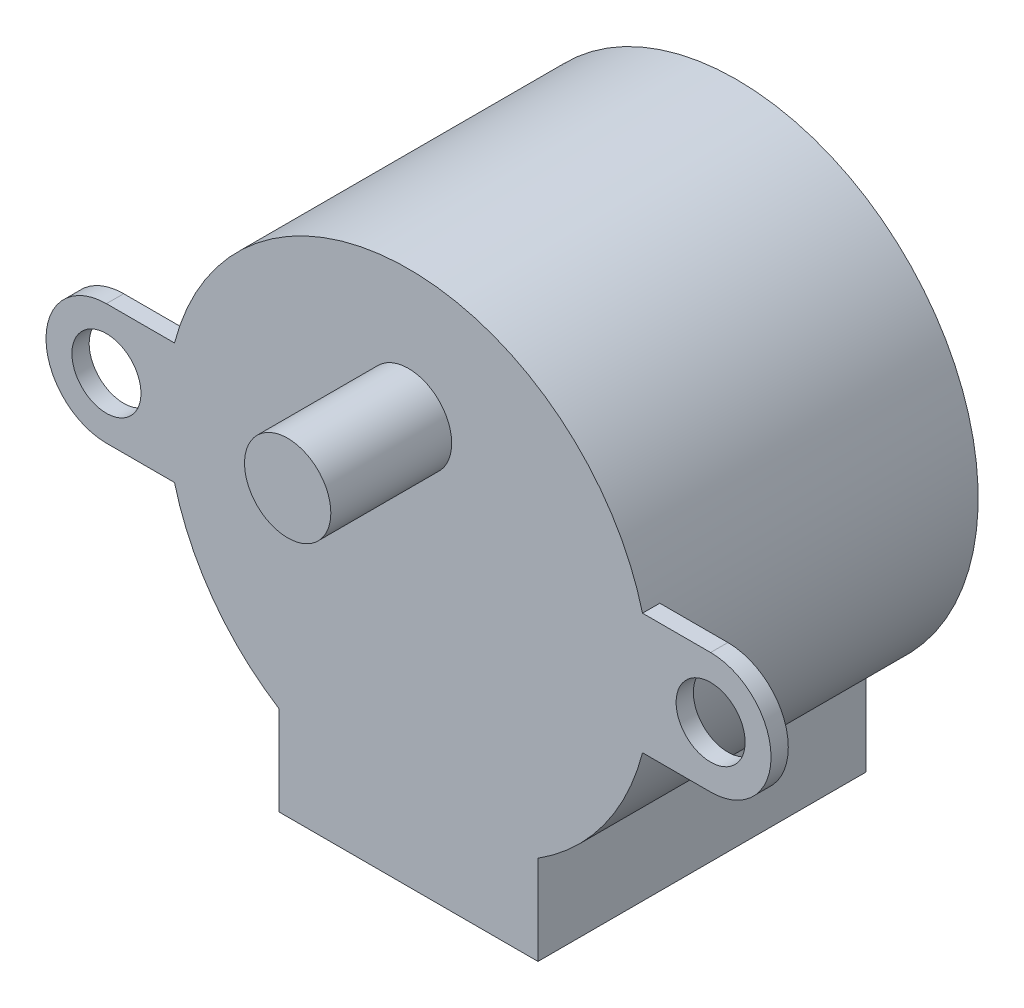
SolidWorks part; units mm, degrees
ref_plane "Plano frontal" through (0, 0, 0) normal (0, 0, 1) x (1, 0, 0)
ref_plane "Plano superior" through (0, 0, 0) normal (0, 1, 0) x (1, 0, 0)
ref_plane "Plano direito" through (0, 0, 0) normal (1, 0, 0) x (0, 0, -1)
sketch "Esboço1" plane through (0, 0, 0) normal (0, 0, 1) x (1, 0, 0)
  line L0 (17.5, 0) -> (0, 0) construction
  line L1 (17.5, 3.5) -> (13.5554, 3.5)
  line L2 (-7.5, -14) -> (-7.5, -11.8216)
  line L3 (13.5554, -3.5) -> (17.5, -3.5)
  line L4 (7.5, -14) -> (7.5, -17)
  line L5 (7.5, -17) -> (-7.5, -17)
  line L6 (7.5, -14) -> (7.5, -11.8216)
  line L7 (-7.5, -14) -> (-7.5, -17)
  line L8 (-13.5554, -3.5) -> (-17.5, -3.5)
  line L9 (-17.5, 3.5) -> (-13.5554, 3.5)
  line L10 (0, 0) -> (-17.5, 0) construction
  arc A0 (13.5554, 3.5) -> (-13.5554, 3.5) centre (0, 0) ccw
  arc A1 (17.5, -3.5) -> (17.5, 3.5) centre (17.5, 0) ccw
  circle A2 centre (17.5, 0) radius 2
  arc A3 (7.5, -11.8216) -> (13.5554, -3.5) centre (0, 0) ccw
  circle A4 centre (-17.5, 0) radius 2
  arc A5 (-17.5, -3.5) -> (-17.5, 3.5) centre (-17.5, 0) cw
  arc A6 (-13.5554, -3.5) -> (-7.5, -11.8216) centre (0, 0) ccw
  point P16 (0, -17)
  point P18 (-7.5, -15.5)
  dimension "D1" = 14
  dimension "D4" = 3.5
  dimension "D2" = 15
  dimension "D3" = 17
  dimension "D5" = 35
extrude "Ressalto-extrusão1" add sketch "Esboço1" along normal blind 19
sketch "Esboço2" plane through (0, 0, 0) normal (0, 0, -1) x (-1, 0, 0)
  line L1 (13.5554, 3.5) -> (23.807, 3.5)
  line L3 (13.5554, -3.5) -> (23.807, -3.5)
  line L4 (23.807, 3.5) -> (23.807, -3.5)
  line L5 (-13.5554, 3.5) -> (-24.7605, 3.5)
  line L7 (-13.5554, -3.5) -> (-24.7605, -3.5)
  line L8 (-24.7605, 3.5) -> (-24.7605, -3.5)
  arc A0 (13.5554, -3.5) -> (13.5554, 3.5) centre (0, 0) ccw
  arc A1 (-13.5554, 3.5) -> (-13.5554, -3.5) centre (0, 0) ccw
extrude "Corte-extrusão1" cut sketch "Esboço2" against normal blind 18
sketch "Esboço3" plane through (0, 0, 19) normal (0, 0, 1) x (1, 0, 0)
  line L0 (-13.5554, 3.5) -> (13.5554, 3.5) construction
  line L1 (0, 3.5) -> (0, 6.5) construction
  circle A0 centre (0, 6.5) radius 2.5
extrude "Ressalto-extrusão2" add sketch "Esboço3" along normal blind 7
